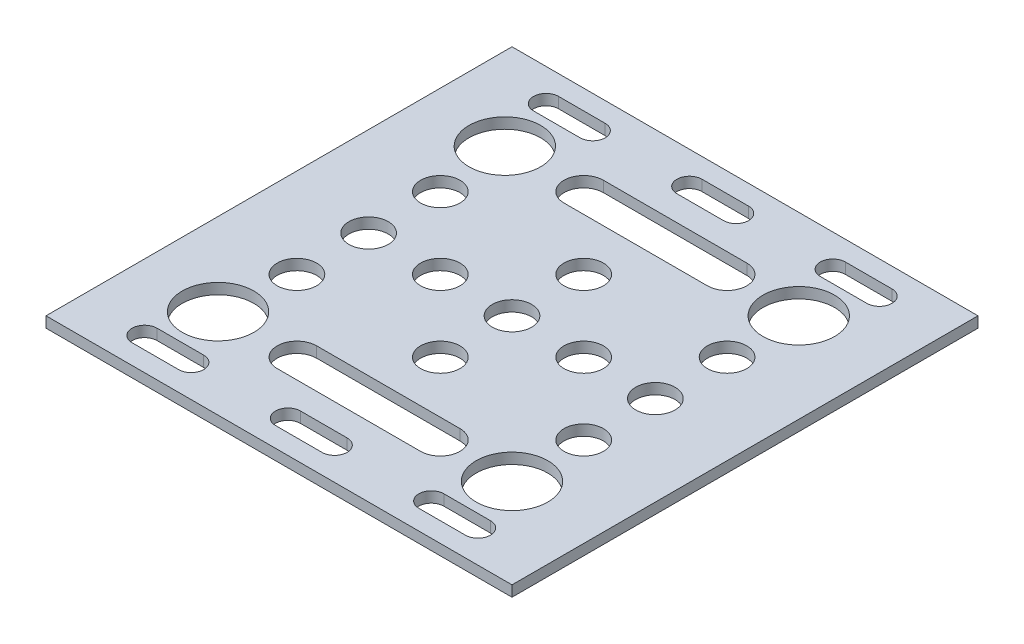
SolidWorks part; units mm, degrees
ref_plane "Front Plane" through (0, 0, 0) normal (0, 0, 1) x (1, 0, 0)
ref_plane "Top Plane" through (0, 0, 0) normal (0, 1, 0) x (1, 0, 0)
ref_plane "Right Plane" through (0, 0, 0) normal (1, 0, 0) x (0, 0, -1)
sketch "Sketch1" plane through (0, 0, 0) normal (0, 1, 0) x (1, 0, 0)
  line L0 (0, 32.5) -> (12.5, 32.5) construction
  line L1 (0, 0) -> (65, 0)
  line L2 (0, 0) -> (0, 65)
  line L3 (0, 65) -> (65, 65)
  line L4 (65, 0) -> (65, 65)
  line L5 (32.5, 65) -> (32.5, 42.5) construction
  line L6 (32.5, 65) -> (32.5, 52.5) construction
  line L7 (32.5, 65) -> (32.5, 60.5) construction
  line L8 (0, 32.5) -> (22.5, 32.5) construction
  line L9 (0, 32.5) -> (65, 32.5) construction
  line L10 (12.5, 32.5) -> (12.5, 42.5) construction
  line L11 (12.5, 42.5) -> (32.5, 42.5) construction
  line L12 (22.5, 52.5) -> (42.5, 52.5) construction
  line L13 (22.5, 55.25) -> (42.5, 55.25)
  line L14 (22.5, 49.75) -> (42.5, 49.75)
  line L15 (29.25, 60.5) -> (35.75, 60.5) construction
  line L16 (29.25, 62.25) -> (35.75, 62.25)
  line L17 (29.25, 58.75) -> (35.75, 58.75)
  line L18 (12.5, 42.5) -> (12.5, 60.5) construction
  line L19 (12.5, 60.5) -> (32.5, 60.5) construction
  line L20 (9.25, 60.5) -> (15.75, 60.5) construction
  line L21 (9.25, 62.25) -> (15.75, 62.25)
  line L22 (9.25, 58.75) -> (15.75, 58.75)
  line L23 (32.5, 52.5) -> (11.5, 52.5) construction
  line L24 (32.5, 65) -> (32.5, 0) construction
  line L25 (55.75, 60.5) -> (49.25, 60.5) construction
  line L26 (55.75, 62.25) -> (49.25, 62.25)
  line L27 (55.75, 58.75) -> (49.25, 58.75)
  line L28 (22.5, 12.5) -> (42.5, 12.5) construction
  line L29 (22.5, 9.75) -> (42.5, 9.75)
  line L30 (22.5, 15.25) -> (42.5, 15.25)
  line L31 (55.75, 4.5) -> (49.25, 4.5) construction
  line L32 (55.75, 2.75) -> (49.25, 2.75)
  line L33 (55.75, 6.25) -> (49.25, 6.25)
  line L34 (9.25, 4.5) -> (15.75, 4.5) construction
  line L35 (9.25, 2.75) -> (15.75, 2.75)
  line L36 (9.25, 6.25) -> (15.75, 6.25)
  line L37 (29.25, 4.5) -> (35.75, 4.5) construction
  line L38 (29.25, 2.75) -> (35.75, 2.75)
  line L39 (29.25, 6.25) -> (35.75, 6.25)
  line L40 (32.5, 52.5) -> (52.5, 52.5) construction
  circle A0 centre (32.5, 32.5) radius 2.75
  circle A1 centre (22.5, 32.5) radius 2.75
  circle A2 centre (12.5, 32.5) radius 2.75
  circle A3 centre (32.5, 42.5) radius 2.75
  circle A4 centre (12.5, 42.5) radius 2.75
  arc A5 (22.5, 55.25) -> (22.5, 49.75) centre (22.5, 52.5) ccw
  arc A6 (42.5, 49.75) -> (42.5, 55.25) centre (42.5, 52.5) ccw
  arc A7 (29.25, 62.25) -> (29.25, 58.75) centre (29.25, 60.5) ccw
  arc A8 (35.75, 58.75) -> (35.75, 62.25) centre (35.75, 60.5) ccw
  arc A9 (9.25, 62.25) -> (9.25, 58.75) centre (9.25, 60.5) ccw
  arc A10 (15.75, 58.75) -> (15.75, 62.25) centre (15.75, 60.5) ccw
  circle A11 centre (11.5, 52.5) radius 5
  circle A12 centre (42.5, 32.5) radius 2.75
  circle A13 centre (52.5, 32.5) radius 2.75
  circle A14 centre (52.5, 42.5) radius 2.75
  arc A16 (55.75, 62.25) -> (55.75, 58.75) centre (55.75, 60.5) cw
  arc A17 (49.25, 58.75) -> (49.25, 62.25) centre (49.25, 60.5) cw
  circle A18 centre (52.5, 22.5) radius 2.75
  circle A19 centre (32.5, 22.5) radius 2.75
  circle A20 centre (12.5, 22.5) radius 2.75
  arc A22 (22.5, 9.75) -> (22.5, 15.25) centre (22.5, 12.5) cw
  arc A23 (42.5, 15.25) -> (42.5, 9.75) centre (42.5, 12.5) cw
  arc A24 (55.75, 2.75) -> (55.75, 6.25) centre (55.75, 4.5) ccw
  arc A25 (49.25, 6.25) -> (49.25, 2.75) centre (49.25, 4.5) ccw
  arc A26 (9.25, 2.75) -> (9.25, 6.25) centre (9.25, 4.5) cw
  arc A27 (15.75, 6.25) -> (15.75, 2.75) centre (15.75, 4.5) cw
  arc A28 (29.25, 2.75) -> (29.25, 6.25) centre (29.25, 4.5) cw
  arc A29 (35.75, 6.25) -> (35.75, 2.75) centre (35.75, 4.5) cw
  circle A30 centre (11.5, 12.5) radius 5
  circle A31 centre (52.5, 52.5) radius 5
  circle A32 centre (52.5, 12.5) radius 5
  point P22 (32.5, 52.5)
  point P27 (19.75, 52.5)
  point P28 (45.25, 52.5)
  point P31 (32.5, 60.5)
  point P36 (27.5, 60.5)
  point P37 (37.5, 60.5)
  point P41 (12.5, 60.5)
  point P46 (7.5, 60.5)
  point P47 (17.5, 60.5)
  point P61 (52.5, 60.5)
  point P76 (32.5, 12.5)
  point P83 (52.5, 4.5)
  point P90 (12.5, 4.5)
  point P97 (32.5, 4.5)
  dimension "D8" = 5.5
  dimension "D9" = 5.5
  dimension "D10" = 5.5
  dimension "D11" = 5.5
  dimension "D12" = 5.5
  dimension "D19" = 10
  dimension "D22" = 10
  dimension "D1" = 65
  dimension "D2" = 65
  dimension "D3" = 12.5
  dimension "D4" = 22.5
  dimension "D5" = 12.5
  dimension "D6" = 4.5
  dimension "D7" = 22.5
  dimension "D13" = 25.5
  dimension "D14" = 5.5
  dimension "D15" = 3.5
  dimension "D16" = 10
  dimension "D17" = 10
  dimension "D18" = 3.5
  dimension "D20" = 21
  dimension "D21" = 20
extrude "Boss-Extrude1" add sketch "Sketch1" along normal blind 1.5
